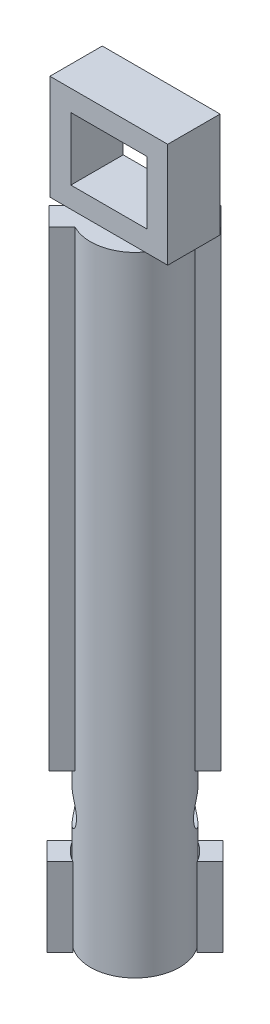
SolidWorks part; units mm, degrees
ref_plane "Front Plane" through (0, 0, 0) normal (0, 0, 1) x (1, 0, 0)
ref_plane "Top Plane" through (0, 0, 0) normal (0, 1, 0) x (1, 0, 0)
ref_plane "Right Plane" through (0, 0, 0) normal (1, 0, 0) x (0, 0, -1)
sketch "Sketch1" plane through (0, 0, 0) normal (0, 1, 0) x (1, 0, 0)
  circle A0 centre (0, 0) radius 1.7
  dimension "D1" = 3.4
extrude "main body" add sketch "Sketch1" along normal mid plane 24
sketch "Sketch2" plane through (0, 12, 0) normal (0, 1, 0) x (1, 0, 0)
  line L0 (3.2385, 3.2385) -> (-4.1755, -4.1755) construction
  line L1 (-0.7954, -1.5025) -> (-1.2903, -1.9974)
  line L2 (-1.2903, -1.9974) -> (-1.9974, -1.2903)
  line L3 (-1.9974, -1.2903) -> (-1.5025, -0.7954)
  line L4 (-1.9627, 1.9627) -> (2.0335, -2.0335) construction
  line L5 (1.2903, 1.9974) -> (0.7954, 1.5025)
  line L6 (1.9974, 1.2903) -> (1.2903, 1.9974)
  line L7 (1.5025, 0.7954) -> (1.9974, 1.2903)
  arc A0 (-1.5025, -0.7954) -> (-0.7954, -1.5025) centre (0, 0) ccw
  arc A1 (0.7954, 1.5025) -> (1.5025, 0.7954) centre (0, 0) cw
  circle A2 centre (0, 0) radius 1.7 construction
  point P8 (-1.0428, -1.75)
  dimension "D1" = 1
  dimension "D2" = 0.7
extrude "top guides" add sketch "Sketch2" against normal blind 18
ref_plane "Plane1" through (-1.6439, 0, 1.6439) normal (-0.7071, 0, 0.7071) x (0.7071, 0, 0.7071)
hole_wizard "M1.6 Tapped Hole2" [suppressed] positions "Sketch5" profile "Sketch6" tap size "M1.6" standard "ISO"
sketch "Sketch5" plane through (-1.6808, 0, 1.6808) normal (-0.7071, 0, 0.7071) x (0.7071, 0, 0.7071)
  line L0 (0, -6.575) -> (0, -13.0742)
  line L2 (-0.502, -13.0742) -> (0.5136, -13.0742)
  dimension "D1" = 6.4992
sketch "Sketch6" plane through (-1.6808, -6.575, 1.6808) normal (0, 1, 0) x (0.7071, 0, 0.7071)
  line L0 (0, 0) -> (0, 4.3755)
  line L1 (0, 4.3755) -> (0.625, 4)
  line L2 (0.625, 4) -> (0.625, 0)
  line L5 (0.625, 0) -> (0, 0)
  line L10 (0, 4.3755) -> (-0.625, 4) construction
  line L11 (0, -6.35) -> (0, 107.95) construction
  dimension "Tap Drill Dia." = 1.25
  dimension "Tap Drill Depth" = 4
  dimension "Drill Angle" = 118
cosmetic thread "Hole Thread3" [suppressed] parameters "D1"=3.2, "D2"=1.6
sketch "Sketch7" plane through (0, -12, 0) normal (0, -1, 0) x (1, 0, 0)
  line L0 (-4.9913, 4.9913) -> (2.4311, -2.4311) construction
  line L1 (1.5394, -0.8323) -> (2.0344, -1.3273)
  line L2 (2.0344, -1.3273) -> (1.3273, -2.0344)
  line L3 (1.3273, -2.0344) -> (0.8323, -1.5394)
  line L4 (-1.9649, -1.9649) -> (2.0358, 2.0358) construction
  line L5 (-2.0344, 1.3273) -> (-1.5394, 0.8323)
  line L6 (-1.3273, 2.0344) -> (-2.0344, 1.3273)
  line L7 (-0.8323, 1.5394) -> (-1.3273, 2.0344)
  arc A0 (0.8323, -1.5394) -> (1.5394, -0.8323) centre (0, 0) ccw
  arc A1 (-1.5394, 0.8323) -> (-0.8323, 1.5394) centre (0, 0) cw
  circle A2 centre (0, 0) radius 1.75
  circle A5 centre (0, 0) radius 1.7 construction
  point P8 (1.7869, -1.0798)
  circle M6 centre (0, 0) radius 1.7
  dimension "D3" = 3.5
  dimension "D1" = 1
  dimension "D2" = 0.7
extrude "bottom guides" add sketch "Sketch7" against normal blind 3 contours L7 L6 L5 M6 | L3 L2 L1 M6
sketch "Sketch10" plane through (0, 12, 0) normal (0, 1, 0) x (1, 0, 0)
  line L1 (2.25, 1) -> (-2.25, 1)
  line L2 (2.25, 1) -> (2.25, -1)
  line L3 (2.25, -1) -> (-2.25, -1)
  line L4 (-2.25, 1) -> (-2.25, -1)
  line L5 (2.25, 1) -> (-2.25, -1) construction
  line L6 (2.25, -1) -> (-2.25, 1) construction
  point P0 (0, 0)
  dimension "D1" = 4.5
  dimension "D2" = 2
extrude "hole extrude" add sketch "Sketch10" along normal blind 4
sketch "Sketch11" plane through (0, 0, -1) normal (0, 0, 1) x (1, 0, 0)
  line L0 (0, 16) -> (0, 12.5203) construction
  line L1 (1.45, 15.2) -> (-1.45, 15.2)
  line L2 (1.45, 15.2) -> (1.45, 12.8)
  line L3 (1.45, 12.8) -> (-1.45, 12.8)
  line L4 (-1.45, 15.2) -> (-1.45, 12.8)
  line L5 (-2.25, 12) -> (-1.7071, 12) construction
  line L7 (-2.25, 16) -> (2.25, 16) construction
  line L8 (-2.25, 16) -> (-2.25, 12) construction
  point P6 (0, 12.8)
  dimension "D1" = 0.8
  dimension "D2" = 0.8
  dimension "D3" = 0.8
extrude "hole cut" cut sketch "Sketch11" along normal through all contours L0 L1 L2 L3 | L1 L0 L3 L4
ref_plane "Plane2" through (1.5025, 0, 0) normal (1, 0, 0) x (0, 1, 0)
hole_wizard "M1.6 Tapped Hole4" positions "Sketch13" profile "Sketch12" tap size "M1.6" standard "ISO" end condition through all
sketch "Sketch13" plane through (-1.6439, 0, 1.6439) normal (-0.7071, 0, 0.7071) x (0.7071, 0, 0.7071)
  line L0 (-1.7, -12) -> (1.7, -12) construction
  line L1 (-1.7, 12) -> (-1.7, -12) construction
  point P0 (0, -7.5)
  dimension "D1" = 4.5
  dimension "D2" = 1.7
sketch "Sketch12" plane through (-1.6439, -7.5, 1.6439) normal (0, 1, 0) x (0.7071, 0, 0.7071)
  line L0 (0, 0) -> (0, 5.3282)
  line L1 (0, 5.3282) -> (0.625, 5.3282)
  line L2 (0.625, 5.3282) -> (0.625, 0)
  line L5 (0.625, 0) -> (0, 0)
  line L11 (0, -6.35) -> (0, 107.95) construction
  dimension "Thru Tap Drill Dia." = 1.25
  dimension "Thru Tap Drill Depth" = 5.3282
cosmetic thread "Hole Thread5" parameters "D2"=1.6
